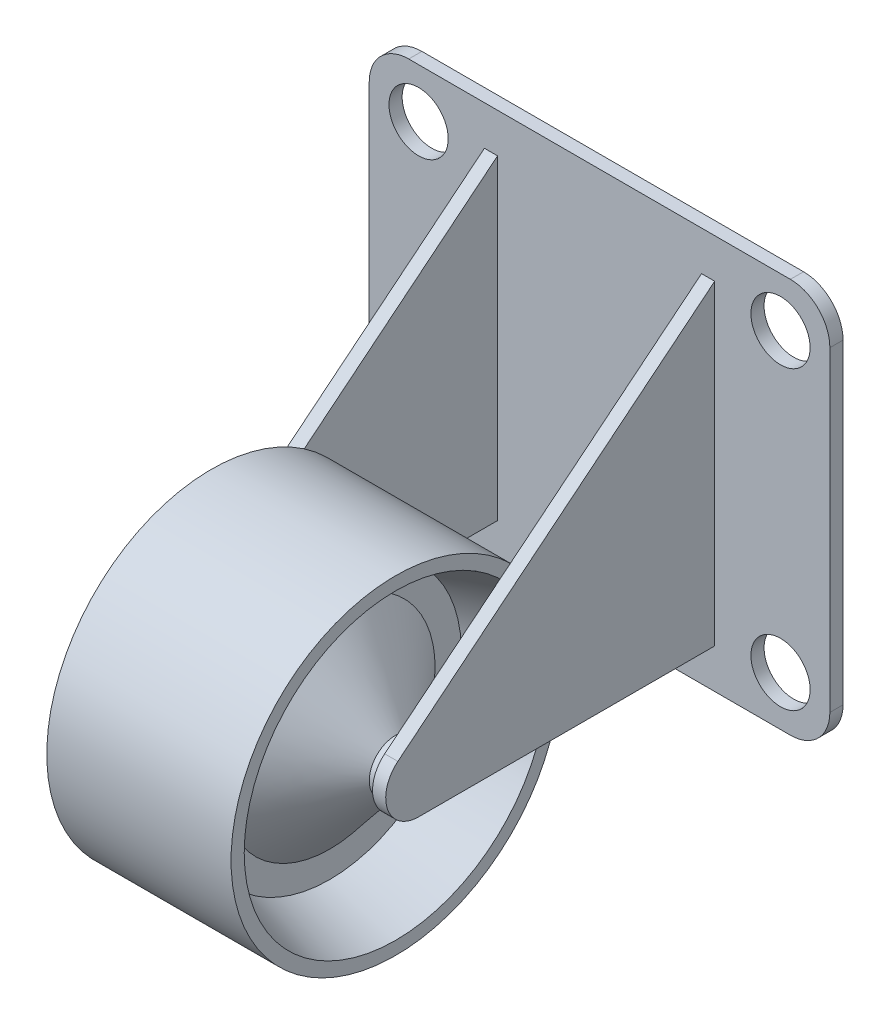
SolidWorks part; units mm, degrees
ref_plane "正面" through (0, 0, 0) normal (0, 0, 1) x (1, 0, 0)
ref_plane "平面" through (0, 0, 0) normal (0, 1, 0) x (1, 0, 0)
ref_plane "右側面" through (0, 0, 0) normal (1, 0, 0) x (0, 0, -1)
sketch "ｽｹｯﾁ1" plane through (0, 0, 0) normal (0, 0, 1) x (1, 0, 0)
  line L1 (0, 0) -> (35, 0)
  line L2 (0, 0) -> (0, -30)
  line L3 (0, -30) -> (35, -30)
  line L4 (35, 0) -> (35, -30)
  dimension "D1" = 30
  dimension "D2" = 35
extrude "ﾎﾞｽ - 押し出し1" add sketch "ｽｹｯﾁ1" along normal blind 1
fillet "ﾌｨﾚｯﾄ1" radius 3 4 edges at (0, -30, 0.5) (35, -30, 0.5) (0, 0, 0.5) (35, 0, 0.5)
sketch "ｽｹｯﾁ2" plane through (0, 0, 1) normal (0, 0, 1) x (1, 0, 0)
  line L0 (3.75, -3.75) -> (3.75, -26.25) construction
  line L1 (3.75, -3.75) -> (31.25, -3.75) construction
  line L2 (32, 0) -> (3, 0) construction
  line L3 (0, -3) -> (0, -27) construction
  circle A0 centre (31.25, -3.75) radius 2.25
  circle A1 centre (31.25, -26.25) radius 2.25
  circle A2 centre (3.75, -26.25) radius 2.25
  circle A3 centre (3.75, -3.75) radius 2.25
  point P8 (17.5, -3.75)
  point P11 (17.5, 0)
  point P12 (3.75, -15)
  point P15 (0, -15)
  dimension "D2" = 4.5
  dimension "D3" = 4.5
  dimension "D4" = 4.5
  dimension "D5" = 4.5
  dimension "D1" = 27.5
  dimension "D6" = 22.5
extrude "ｶｯﾄ - 押し出し1" cut sketch "ｽｹｯﾁ2" against normal through all
sketch "ｽｹｯﾁ3" plane through (0, 0, 0) normal (0, 1, 0) x (1, 0, 0)
  line L0 (8.75, -1) -> (8.75, -26)
  line L1 (32, -1) -> (3, -1) construction
  line L2 (8.75, -26) -> (9.75, -26)
  line L3 (9.75, -26) -> (9.75, -1)
  line L4 (9.75, -1) -> (8.75, -1)
  line L5 (25.25, -1) -> (25.25, -26)
  line L6 (25.25, -26) -> (26.25, -26)
  line L7 (26.25, -26) -> (26.25, -1)
  line L8 (26.25, -1) -> (25.25, -1)
  line L9 (9.75, -7.7317) -> (25.25, -7.7317) construction
  point P12 (17.5, -7.7317)
  point P13 (17.5, -1)
  dimension "D1" = 25
  dimension "D2" = 25
  dimension "D3" = 1
  dimension "D4" = 1
  dimension "D5" = 17.5
extrude "ﾎﾞｽ - 押し出し2" add sketch "ｽｹｯﾁ3" against normal up to vertex (30 mm away)
sketch "ｽｹｯﾁ4" plane through (26.25, 0, 0) normal (1, 0, 0) x (0, 0, -1)
  line L0 (-25.0764, -22.5596) -> (-1, -3)
  line L1 (-1, -30) -> (-1, 0) construction
  line L2 (-1, -3) -> (-1, 0)
  line L3 (-1, 0) -> (-26, 0)
  line L4 (-26, 0) -> (-26, -30)
  line L5 (-26, -30) -> (-1, -30)
  line L6 (-1, -30) -> (-1, -27)
  line L7 (-1, -27) -> (-23.5, -27)
  arc A0 (-25.0764, -22.5596) -> (-23.5, -27) centre (-23.5, -24.5) ccw
  line M1 (-1, 0) -> (-26, 0)
  line M2 (-26, 0) -> (-26, -30)
  line M3 (-26, -30) -> (-1, -30)
  line M4 (-1, -30) -> (-1, 0)
  dimension "D1" = 22.5
  dimension "D2" = 3
  dimension "D3" = 3
extrude "ｶｯﾄ - 押し出し2" cut sketch "ｽｹｯﾁ4" against normal through all contours A0 L0 M4 M1 M2 | A0 L4 L7 M3 M4
sketch "ｽｹｯﾁ5" plane through (25.25, 0, 0) normal (-1, 0, 0) x (0, 0, 1)
  circle A0 centre (23.5, -24.5) radius 2
  dimension "D1" = 4
extrude "ﾎﾞｽ - 押し出し3" add sketch "ｽｹｯﾁ5" along normal up to next
ref_plane "平面1" through (0, 0, 23.5) normal (0, 0, -1) x (-1, 0, 0)
ref_plane "平面2" through (17.5, 0, 0) normal (1, 0, 0) x (0, 0, -1)
sketch "ｽｹｯﾁ6" plane through (17.5, 0, 0) normal (1, 0, 0) x (0, 0, -1)
  line L0 (-23.5, -16.5) -> (-23.5, 16.5) construction
  circle A0 centre (-23.5, -24.5) radius 12.5
  arc A1 (-25.0764, -22.5596) -> (-23.5, -27) centre (-23.5, -24.5) ccw construction
  dimension "D1" = 25
extrude "ﾎﾞｽ - 押し出し4" add sketch "ｽｹｯﾁ6" along normal mid plane 14
sketch "ｽｹｯﾁ7" plane through (0, 0, 23.5) normal (0, 0, -1) x (-1, 0, 0)
  line L0 (-24.5, -13) -> (-19.5, -14.5)
  line L1 (-24.5, -12) -> (-24.5, -37) construction
  line L2 (-19.5, -14.5) -> (-19.5, -16.5)
  line L3 (-19.5, -16.5) -> (-24.5, -22.5)
  line L4 (-24.5, -22.5) -> (-24.5, -13)
  line L5 (-10.5, -13) -> (-15.5, -14.5)
  line L6 (-10.5, -37) -> (-10.5, -12) construction
  line L7 (-15.5, -14.5) -> (-15.5, -16.5)
  line L8 (-15.5, -16.5) -> (-10.5, -22.5)
  line L9 (-10.5, -22.5) -> (-10.5, -13)
  line L10 (9.094, -24.5) -> (-41.1502, -24.5) construction
  line L11 (-24.5, -22.5) -> (-25.25, -22.5) construction
  dimension "D1" = 1
  dimension "D2" = 1
  dimension "D3" = 5
  dimension "D4" = 5
  dimension "D5" = 2
  dimension "D6" = 2
  dimension "D7" = 2
  dimension "D8" = 16
  dimension "D9" = 16
revolve "ｶｯﾄ - 回転1" cut sketch "ｽｹｯﾁ7" angle 360 about L10
